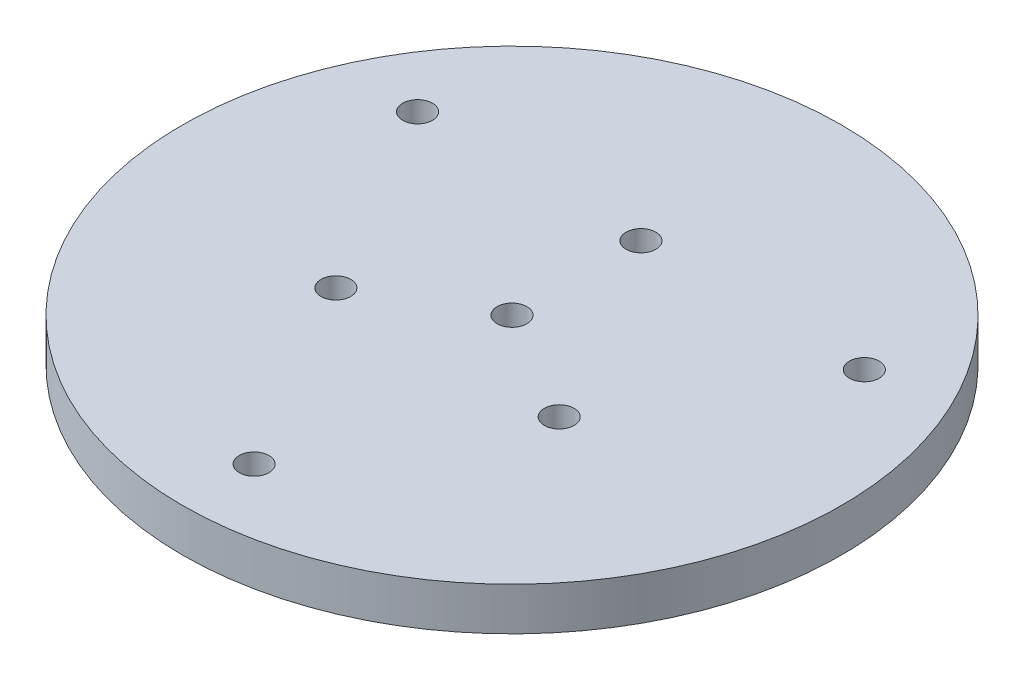
SolidWorks part; units mm, degrees
material "6061-T6 (SS)"
ref_plane "Front Plane" through (0, 0, 0) normal (0, 0, 1) x (1, 0, 0)
ref_plane "Top Plane" through (0, 0, 0) normal (0, 1, 0) x (1, 0, 0)
ref_plane "Right Plane" through (0, 0, 0) normal (1, 0, 0) x (0, 0, -1)
sketch "Sketch1" plane through (0, 0, 0) normal (0, 1, 0) x (1, 0, 0)
  line L0 (-49.4934, 28.575) -> (0, -57.15) construction
  line L1 (0, -57.15) -> (49.4934, 28.575) construction
  line L2 (49.4934, 28.575) -> (-49.4934, 28.575) construction
  circle A0 centre (0, 0) radius 73.025
  circle A1 centre (0, 0) radius 3.3
  circle A2 centre (0, 25.4) radius 1.5875 construction
  circle A3 centre (0, 0) radius 57.15 construction
  circle A4 centre (0, -57.15) radius 3.3
  circle A5 centre (-49.4934, 28.575) radius 3.3
  circle A6 centre (49.4934, 28.575) radius 3.3
  circle A7 centre (0, 0) radius 28.575 construction
  circle A8 centre (24.7467, -14.2875) radius 3.3
  circle A9 centre (-24.7467, -14.2875) radius 3.3
  circle A10 centre (0, 28.575) radius 3.3
  point P16 (0, 0)
  point P25 (0, 0)
  dimension "D1" = 146.05
  dimension "D2" = 6.6
  dimension "D3" = 3.175
  dimension "D5" = 114.3
  dimension "D6" = 6.6
  dimension "D8" = 6.6
  dimension "D4" = 25.4
  dimension "D10" = 28.575
  dimension "D7" = 3
  dimension "D9" = 3
extrude "Boss-Extrude1" add sketch "Sketch1" along normal mid plane 9.525
ref_plane "Plane1" through (0, 0, 76.2) normal (0, 0, 1) x (1, 0, 0)
sketch "Sketch5" plane through (0, 0, 76.2) normal (0, 0, 1) x (1, 0, 0)
  circle A0 centre (0, 0) radius 2
  dimension "D1" = 4
extrude "Cut-Extrude1" [suppressed] cut sketch "Sketch5" against normal blind 19.05
sketch "Sketch14" plane through (0, 0, 0) normal (0, 0, 1) x (1, 0, 0)
  line L0 (0, -5.2723) -> (0, 5.2496)
pattern_circular "CirPattern5" [suppressed] count 4 over 360 about axis through (0, -5.2723, 0) along (0, 1, 0)
